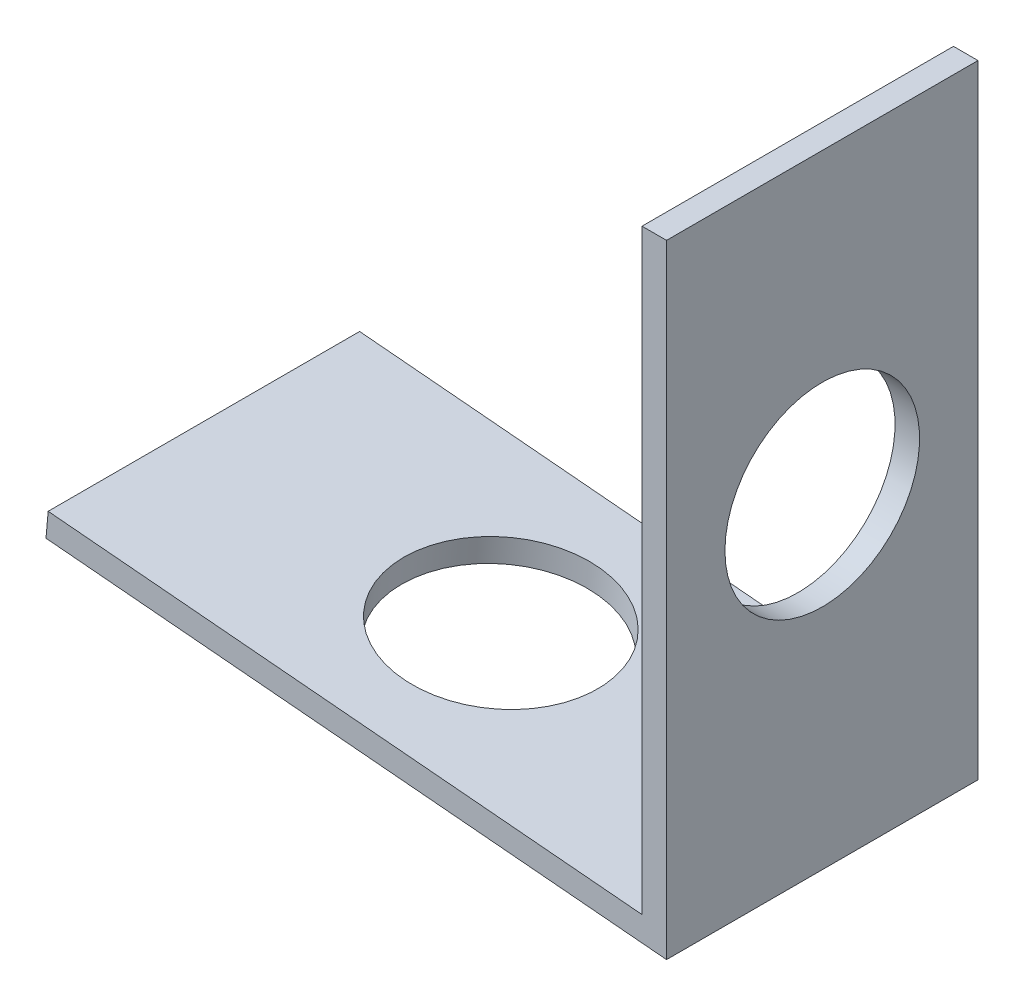
SolidWorks part; units mm, degrees
material "6061 Alloy"
ref_plane "Front Plane" through (0, 0, 0) normal (0, 0, 1) x (1, 0, 0)
ref_plane "Top Plane" through (0, 0, 0) normal (0, 1, 0) x (1, 0, 0)
ref_plane "Right Plane" through (0, 0, 0) normal (1, 0, 0) x (0, 0, -1)
sketch "Sketch1" plane through (0, 0, 0) normal (0, 0, 1) x (1, 0, 0)
  line L0 (0, 0) -> (0, 25.4)
  line L1 (0, 0) -> (-25.302, 2.2291)
  line L2 (-1, 1.092) -> (-25.2142, 3.2253)
  line L3 (-1, 1.092) -> (-1, 25.4)
  line L4 (-25.2142, 3.2253) -> (-25.302, 2.2291)
  line L5 (-1, 25.4) -> (0, 25.4)
  dimension "D1" = 25.4
  dimension "D2" = 84.965
  dimension "D3" = 25.4
  dimension "D4" = 1
extrude "Boss-Extrude1" add sketch "Sketch1" along normal mid plane 12.7
sketch "Sketch7" plane through (-1, 0, 0) normal (-1, 0, 0) x (0, 0, 1)
  line L0 (-6.35, 13.246) -> (6.35, 13.246) construction
  line L1 (-6.35, 25.4) -> (-6.35, 1.092) construction
  line L2 (6.35, 25.4) -> (6.35, 1.092) construction
  line L3 (0, 25.4) -> (0, 1.092) construction
  line L4 (6.35, 25.4) -> (-6.35, 25.4) construction
  line L5 (6.35, 1.092) -> (-6.35, 1.092) construction
  point P12 (0, 13.246)
hole_wizard "5/16 (0.3125) Diameter Hole1" positions "3DSketch1" profile "Sketch8" hole size "5/16" standard "ANSI Inch" end condition through all
sketch3d "3DSketch1"
  point P0 (-1, 13.246, 0)
sketch "Sketch8" plane through (-1, 13.246, 0) normal (0, 1, 0) x (0, 0, 1)
  line L0 (0, 0) -> (0, 1)
  line L1 (0, 1) -> (3.9688, 1)
  line L2 (3.9688, 1) -> (3.9687, 0)
  line L5 (3.9687, 0) -> (0, 0)
  line L11 (0, -6.35) -> (0, 107.95) construction
  dimension "Thru Hole Dia." = 7.9375
  dimension "Thru Hole Depth" = 1
sketch "Sketch9" plane through (0.0878, 0.9961, 0) normal (0.0878, 0.9961, 0) x (0.9961, -0.0878, 0)
  line L0 (-13.246, 6.35) -> (-13.246, -6.35) construction
  line L1 (-1.092, 6.35) -> (-25.4, 6.35) construction
  line L2 (-1.092, -6.35) -> (-25.4, -6.35) construction
  line L3 (-25.4, 0) -> (-1.092, 0) construction
  line L4 (-25.4, -6.35) -> (-25.4, 6.35) construction
  line L5 (-1.092, -6.35) -> (-1.092, 6.35) construction
  point P12 (-13.246, 0)
hole_wizard "5/16 (0.3125) Diameter Hole2" positions "3DSketch2" profile "Sketch10" hole size "5/16" standard "ANSI Inch" end condition through all
sketch3d "3DSketch2"
  point P0 (-13.1071, 2.1586, 0)
sketch "Sketch10" plane through (-13.1071, 2.1586, 0) normal (0, 0, 1) x (-0.9961, 0.0878, 0)
  line L0 (0, 0) -> (0, 3.2205)
  line L1 (0, 3.2205) -> (3.9687, 3.2205)
  line L2 (3.9687, 3.2205) -> (3.9687, 0)
  line L5 (3.9687, 0) -> (0, 0)
  line L11 (0, -6.35) -> (0, 107.95) construction
  dimension "Thru Hole Dia." = 7.9375
  dimension "Thru Hole Depth" = 3.2205
